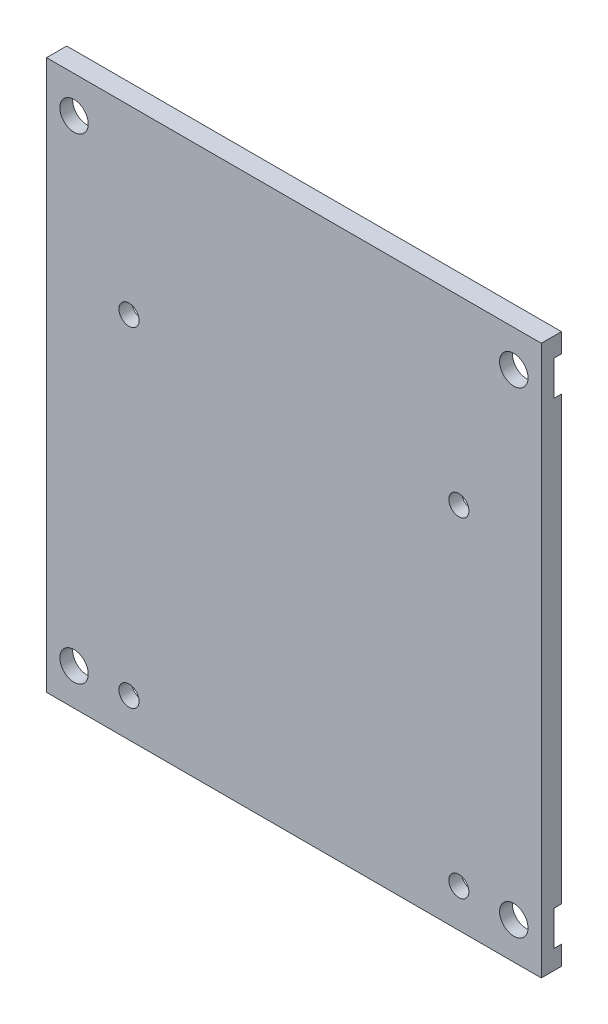
SolidWorks part; units mm, degrees
ref_plane "前视基准面" through (0, 0, 0) normal (0, 0, 1) x (1, 0, 0)
ref_plane "上视基准面" through (0, 0, 0) normal (0, 1, 0) x (1, 0, 0)
ref_plane "右视基准面" through (0, 0, 0) normal (1, 0, 0) x (0, 0, -1)
sketch "草图1" plane through (0, 0, 0) normal (0, 0, 1) x (1, 0, 0)
  line L1 (-27, 30) -> (27, 30)
  line L2 (-27, 30) -> (-27, -30)
  line L3 (-27, -30) -> (27, -30)
  line L4 (27, 30) -> (27, -30)
  line L5 (-27, 30) -> (27, -30) construction
  line L6 (-27, -30) -> (27, 30) construction
  circle A0 centre (-18, -25.8) radius 1.1
  circle A1 centre (18, -25.8) radius 1.1
  circle A2 centre (-18, 10.2) radius 1.1
  circle A3 centre (18, 10.2) radius 1.1
  point P0 (0, 0)
  dimension "D3" = 2.2
  dimension "D4" = 2.2
  dimension "D5" = 2.2
  dimension "D6" = 2.2
  dimension "D1" = 60
  dimension "D2" = 54
  dimension "D7" = 36
  dimension "D8" = 36
  dimension "D9" = 36
  dimension "D10" = 9
  dimension "D11" = 4.2
extrude "凸台-拉伸1" add sketch "草图1" along normal blind 2.2
sketch "草图2" plane through (0, 0, 0) normal (0, 0, -1) x (-1, 0, 0)
  circle A0 centre (-18, 10.2) radius 3
  circle A1 centre (18, 10.2) radius 3
  circle A2 centre (-18, -25.8) radius 2.9296
  circle A3 centre (18, -25.8) radius 3
  dimension "D1" = 6
  dimension "D2" = 6
  dimension "D3" = 5.8591
  dimension "D4" = 6
extrude "切除-拉伸1" cut sketch "草图2" against normal blind 0.8
sketch "草图3" plane through (0, 0, 2.2) normal (0, 0, 1) x (1, 0, 0)
  line L0 (-20, 36.5839) -> (-20, -38.2649) construction
  line L1 (-27, 30) -> (-27, -30) construction
  line L2 (-27, -30) -> (27, -30) construction
  line L3 (27, 30) -> (-27, 30) construction
  line L4 (0, 47.6819) -> (0, -38.2649) construction
  circle A0 centre (-18, -25.8) radius 1.1 construction
  circle A1 centre (-18, -25.8) radius 1.1
  circle A2 centre (-24, -26) radius 1.55
  circle A3 centre (-24, 26) radius 1.55
  circle A4 centre (24, -26) radius 1.55
  circle A5 centre (24, 26) radius 1.55
  dimension "D2" = 3.1
  dimension "D3" = 3.1
  dimension "D1" = 2
  dimension "D4" = 3
  dimension "D5" = 4
  dimension "D6" = 3
  dimension "D7" = 4
extrude "切除-拉伸2" cut sketch "草图3" against normal through all
sketch "草图4" plane through (0, 0, 0) normal (0, 0, -1) x (-1, 0, 0)
  circle A0 centre (24, -26) radius 1.55 construction
  circle A1 centre (-24, -26) radius 1.55 construction
  circle A2 centre (24, 26) radius 1.55 construction
  circle A3 centre (-24, 26) radius 1.55 construction
  circle A4 centre (24, -26) radius 1.55
  circle A5 centre (-24, -26) radius 1.55
  circle A6 centre (24, 26) radius 1.55
  circle A7 centre (-24, 26) radius 1.55
  circle A8 centre (-24, 26) radius 3.55
  circle A9 centre (24, 26) radius 3.55
  circle A10 centre (24, -26) radius 3.55
  circle A11 centre (-24, -26) radius 3.55
  dimension "D1" = 2
extrude "切除-拉伸3" cut sketch "草图4" against normal blind 0.8
